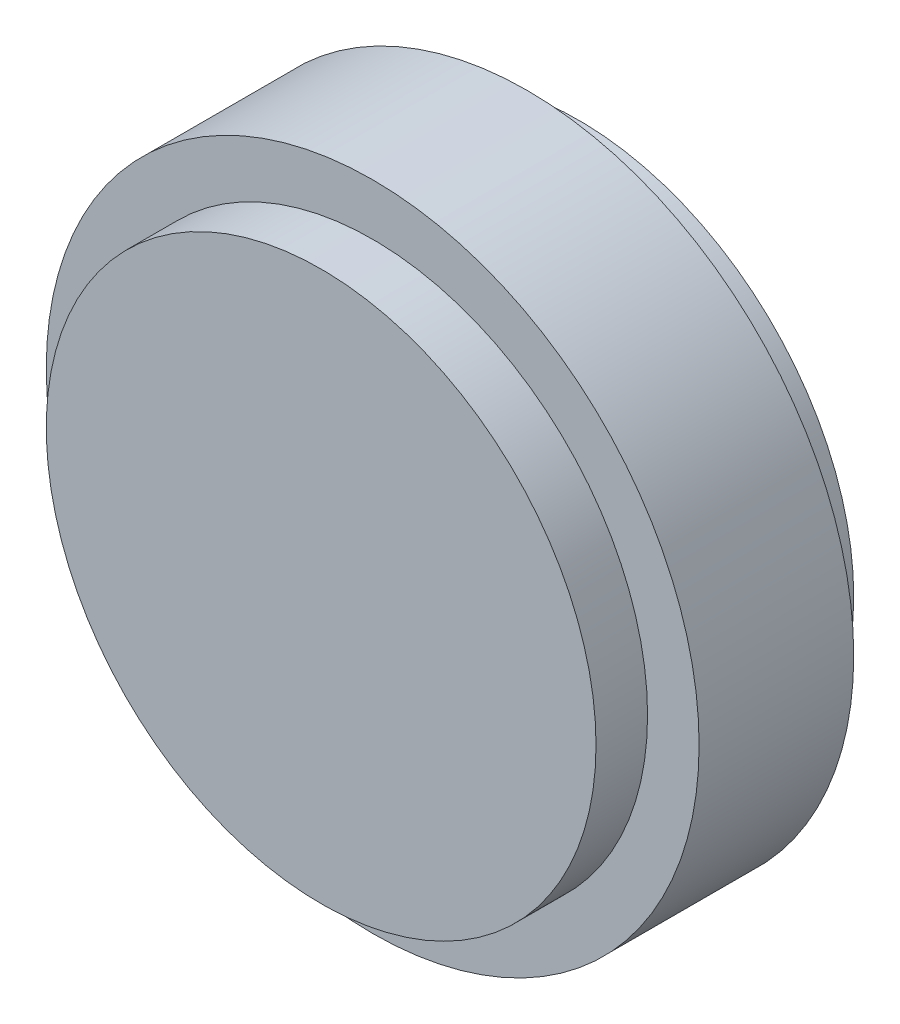
SolidWorks part; units mm, degrees
ref_plane "Front" through (0, 0, 0) normal (0, 0, 1) x (1, 0, 0)
ref_plane "Top" through (0, 0, 0) normal (0, 1, 0) x (1, 0, 0)
ref_plane "Right" through (0, 0, 0) normal (1, 0, 0) x (0, 0, -1)
other "Configuration Table"
sketch "Sketch2" plane through (0, 0, 0) normal (1, 0, 0) x (0, 0, -1)
  line L0 (0, 0) -> (67.6083, 0) construction
  line L1 (7.5, 0) -> (7.5, 19) construction
  line L2 (0, 0) -> (15, 0)
  line L3 (0, 0) -> (0, 16)
  line L4 (0, 16) -> (3, 16)
  line L5 (15, 0) -> (15, 16)
  line L7 (3, 16) -> (3, 19)
  line L8 (3, 19) -> (12, 19)
  line L9 (12, 16) -> (12, 19)
  line L10 (12, 16) -> (15, 16)
  dimension "D1" = 16
  dimension "D2" = 3
  dimension "D3" = 15
revolve "Revolve1" add sketch "Sketch2" angle 360 about L0
